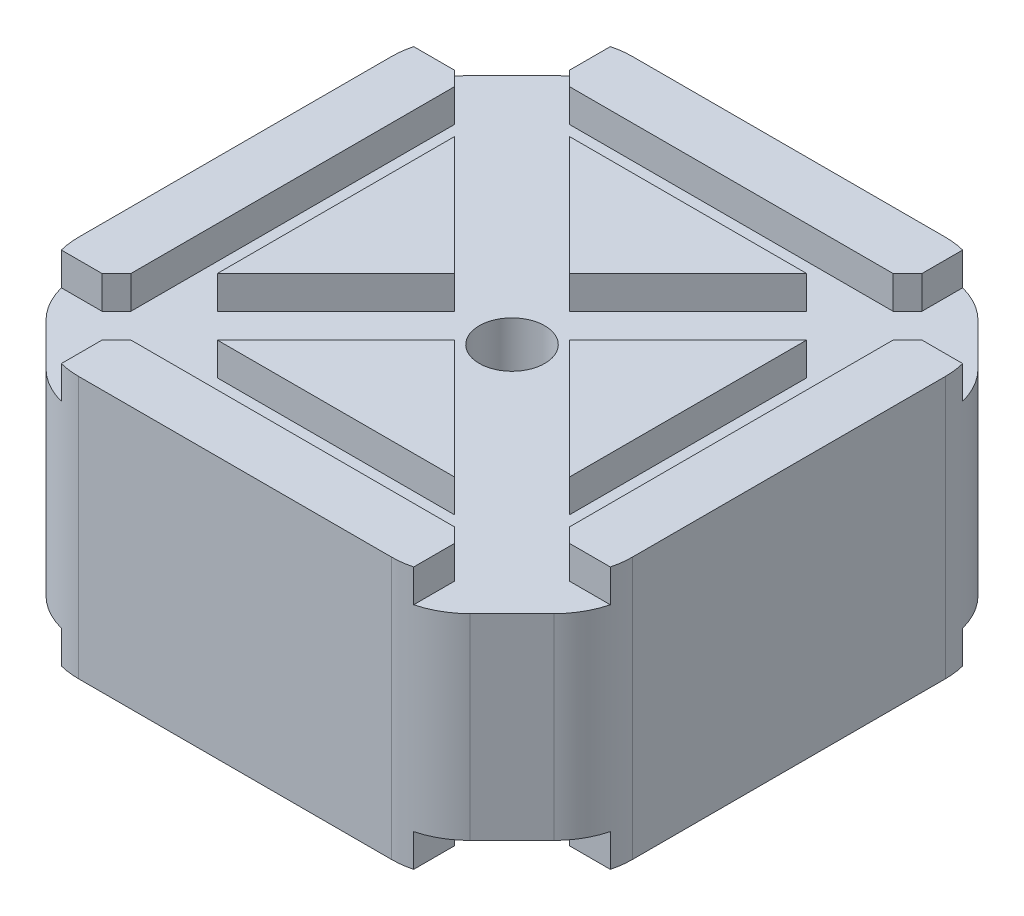
SolidWorks part; units mm, degrees
material "Alumina"
ref_plane "Front Plane" through (0, 0, 0) normal (0, 0, 1) x (1, 0, 0)
ref_plane "Top Plane" through (0, 0, 0) normal (0, 1, 0) x (1, 0, 0)
ref_plane "Right Plane" through (0, 0, 0) normal (1, 0, 0) x (0, 0, -1)
sketch "Sketch1" plane through (0, 0, 0) normal (0, 1, 0) x (1, 0, 0)
  line L0 (-21.15, 16.7509) -> (-16.7509, 21.15)
  line L1 (-16.7509, -21.15) -> (16.7509, -21.15)
  line L2 (-21.15, -16.7509) -> (-21.15, 16.7509)
  line L3 (-16.7509, 21.15) -> (16.7509, 21.15)
  line L4 (21.15, -16.7509) -> (21.15, 16.7509)
  line L7 (16.7509, 21.15) -> (21.15, 16.7509)
  line L8 (16.7509, -21.15) -> (21.15, -16.7509)
  line L9 (-21.15, -16.7509) -> (-16.7509, -21.15)
  point P0 (0, 0)
  dimension "D1" = 42.3
  dimension "D2" = 42.3
  dimension "D3" = 53.6
  dimension "D4" = 45
  dimension "D5" = 45
  dimension "D7" = 53.6
extrude "Boss-Extrude1" add sketch "Sketch1" along normal blind 10
sketch "Sketch18" plane through (0, 0, 21.15) normal (0, 0, 1) x (1, 0, 0)
  line L0 (13.4509, 10) -> (13.4509, 7.5)
  line L1 (-16.7509, 10) -> (16.7509, 10) construction
  line L2 (13.4509, 7.5) -> (16.7509, 7.5)
  line L3 (16.7509, 10) -> (16.7509, 0) construction
  line L4 (16.7509, 7.5) -> (16.7509, 10)
  line L5 (16.7509, 10) -> (13.4509, 10)
  line L6 (-13.4509, 10) -> (-13.4509, 7.5)
  line L7 (-13.4509, 7.5) -> (-16.7509, 7.5)
  line L8 (-16.7509, 10) -> (-16.7509, 0) construction
  line L9 (-16.7509, 7.5) -> (-16.7509, 10)
  line L10 (-16.7509, 10) -> (-13.4509, 10)
  dimension "D1" = 2.5
  dimension "D2" = 2.5
  dimension "D3" = 3.3
  dimension "D4" = 3.3
extrude "Cut-Extrude10" cut sketch "Sketch18" against normal through all
sketch "Sketch19" plane through (21.15, 0, 0) normal (1, 0, 0) x (0, 0, -1)
  line L0 (-13.4509, 10) -> (-13.4509, 7.5)
  line L1 (-16.7509, 10) -> (16.7509, 10) construction
  line L2 (-13.4509, 7.5) -> (-16.7509, 7.5)
  line L3 (-16.7509, 10) -> (-16.7509, 0) construction
  line L4 (-16.7509, 7.5) -> (-16.7509, 10)
  line L5 (-16.7509, 10) -> (-13.4509, 10)
  line L6 (13.4509, 10) -> (13.4509, 7.5)
  line L7 (13.4509, 7.5) -> (16.7509, 7.5)
  line L8 (16.7509, 10) -> (16.7509, 0) construction
  line L9 (16.7509, 7.5) -> (16.7509, 10)
  line L10 (16.7509, 10) -> (13.4509, 10)
  dimension "D1" = 3.3
  dimension "D2" = 3.3
  dimension "D3" = 2.5
  dimension "D4" = 2.5
extrude "Cut-Extrude11" cut sketch "Sketch19" against normal through all
sketch "Sketch20" plane through (18.9505, 0, 18.9505) normal (0.7071, 0, 0.7071) x (0.7071, 0, -0.7071)
  line L0 (-3.1106, 7.5) -> (3.1106, 7.5)
  line L1 (3.1106, 7.5) -> (3.1106, 10)
  line L2 (3.1106, 10) -> (-3.1106, 10)
  line L3 (-3.1106, 10) -> (-3.1106, 7.5)
extrude "Cut-Extrude12" cut sketch "Sketch20" against normal through all
sketch "Sketch21" plane through (-18.9505, 0, 18.9505) normal (-0.7071, 0, 0.7071) x (0.7071, 0, 0.7071)
  line L0 (-3.1106, 7.5) -> (3.1106, 7.5)
  line L1 (3.1106, 7.5) -> (3.1106, 10)
  line L2 (3.1106, 10) -> (-3.1106, 10)
  line L3 (-3.1106, 10) -> (-3.1106, 7.5)
extrude "Cut-Extrude13" cut sketch "Sketch21" against normal through all
sketch "Sketch22" plane through (0, 7.5, 0) normal (0, 1, 0) x (1, 0, 0)
  circle A0 centre (0, 0) radius 2.5
  dimension "D1" = 5
extrude "Cut-Extrude14" cut sketch "Sketch22" against normal through all
mirror "Mirror1" about plane through (0, 0, 0) normal (0, -1, 0) of "Boss-Extrude1", "Cut-Extrude14", "Cut-Extrude13", "Cut-Extrude12", "Cut-Extrude11", "Cut-Extrude10"
sketch "Sketch23" plane through (0, 7.5, 0) normal (0, 1, 0) x (1, 0, 0)
  line L0 (-21.15, -14.4325) -> (-14.4325, -21.15)
  line L1 (-14.4325, -21.15) -> (-16.7509, -21.15)
  line L2 (-16.7509, -21.15) -> (-21.15, -16.7509)
  line L3 (-21.15, -16.7509) -> (-21.15, -14.4325)
  line L4 (-21.15, 14.4325) -> (-14.4325, 21.15)
  line L5 (-14.4325, 21.15) -> (-16.7509, 21.15)
  line L6 (-16.7509, 21.15) -> (-21.15, 16.7509)
  line L7 (-21.15, 16.7509) -> (-21.15, 14.4325)
  line L8 (14.4325, 21.15) -> (21.15, 14.4325)
  line L9 (21.15, 14.4325) -> (21.15, 16.7509)
  line L10 (21.15, 16.7509) -> (16.7509, 21.15)
  line L11 (16.7509, 21.15) -> (14.4325, 21.15)
  line L12 (14.4325, -21.15) -> (21.15, -14.4325)
  line L13 (21.15, -14.4325) -> (21.15, -16.7509)
  line L14 (21.15, -16.7509) -> (16.7509, -21.15)
  line L15 (16.7509, -21.15) -> (14.4325, -21.15)
  dimension "D1" = 9.5
  dimension "D2" = 9.5
  dimension "D3" = 9.5
  dimension "D4" = 9.5
extrude "Cut-Extrude15" cut sketch "Sketch23" against normal through all
fillet "Fillet8" radius 6 8 edges at (14.4325, 0, -21.15) (21.15, 0, -14.4325) (-21.15, 0, -14.4325) (-14.4325, 0, -21.15) (-14.4325, 0, 21.15) (-21.15, 0, 14.4325) (21.15, 0, 14.4325) (14.4325, 0, 21.15)
